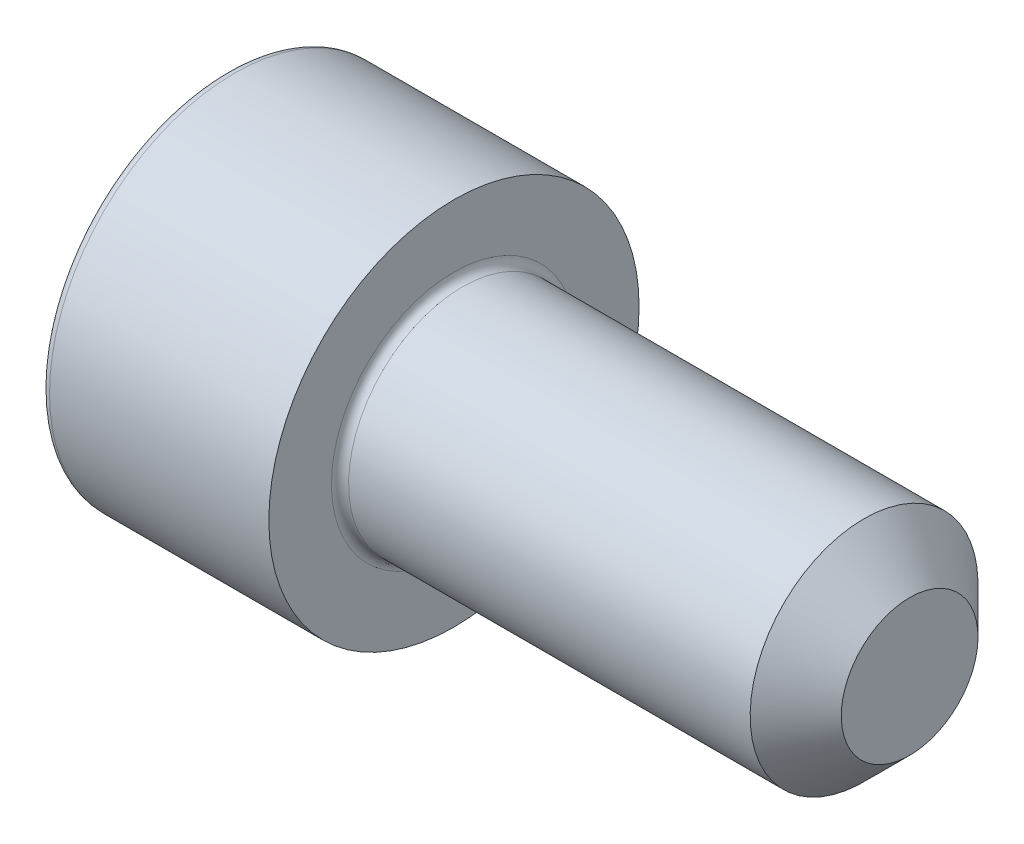
SolidWorks part; units mm, degrees
ref_plane "Спереди" through (0, 0, 0) normal (0, 0, 1) x (1, 0, 0)
ref_plane "Сверху" through (0, 0, 0) normal (0, 1, 0) x (1, 0, 0)
ref_plane "Справа" through (0, 0, 0) normal (1, 0, 0) x (0, 0, -1)
sketch "Эскиз1" plane through (0, 0, 0) normal (0, 0, 1) x (1, 0, 0)
  line L0 (0, 0) -> (0, 6.5)
  line L1 (0, 6.5) -> (8, 6.5)
  line L2 (8, 6.5) -> (8, 4)
  line L3 (8, 4) -> (24, 4)
  line L4 (24, 4) -> (24, 0)
  line L5 (24, 0) -> (0, 0) construction
  line L6 (0, 0) -> (24, 0)
  dimension "D1" = 13
  dimension "D2" = 8
  dimension "D3" = 8
  dimension "D4" = 16
revolve "Повернуть1" add sketch "Эскиз1" angle 360 about L5
cosmetic thread "Условное изображение резьбы1" parameters "D2"=6.619
sketch "Эскиз2" plane through (0, 0, 0) normal (-1, 0, 0) x (0, 0, 1)
  line L1 (-1.7321, 3) -> (-3.4641, 0)
  line L2 (-3.4641, 0) -> (-1.7321, -3)
  line L3 (-1.7321, -3) -> (1.7321, -3)
  line L4 (1.7321, -3) -> (3.4641, 0)
  line L5 (3.4641, 0) -> (1.7321, 3)
  line L6 (1.7321, 3) -> (-1.7321, 3)
  circle A0 centre (0, 0) radius 3 construction
  dimension "D1" = 6
extrude "Вырез-Вытянуть1" cut sketch "Эскиз2" against normal blind 2.5
fillet "Скругление1" radius 0.3 2 edges at (0, 6.5, 0) (8, 4, 0)
chamfer "Фаска1" distance 1.6 angle 45 1 edges at (24, 4, 0)
